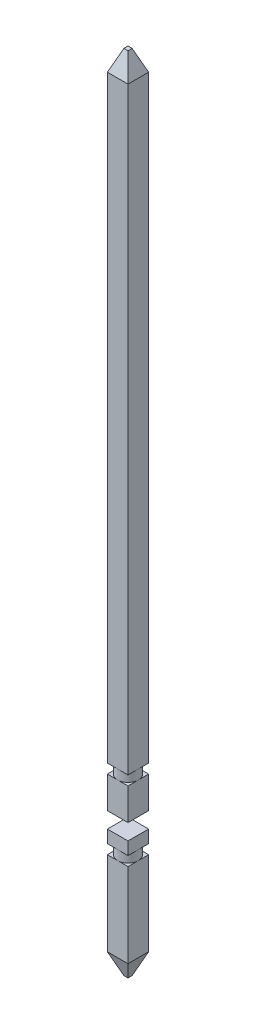
SolidWorks part; units mm, degrees
ref_plane "Front Plane" through (0, 0, 0) normal (0, 0, 1) x (1, 0, 0)
ref_plane "Top Plane" through (0, 0, 0) normal (0, 1, 0) x (1, 0, 0)
ref_plane "Right Plane" through (0, 0, 0) normal (1, 0, 0) x (0, 0, -1)
sketch "Sketch2" plane through (0, 0, 0) normal (0, 1, 0) x (1, 0, 0)
  line L1 (-0.325, -0.325) -> (0.325, -0.325)
  line L2 (-0.325, -0.325) -> (-0.325, 0.325)
  line L3 (-0.325, 0.325) -> (0.325, 0.325)
  line L4 (0.325, -0.325) -> (0.325, 0.325)
  line L5 (-0.325, -0.325) -> (0.325, 0.325) construction
  line L6 (-0.325, 0.325) -> (0.325, -0.325) construction
  point P0 (0, 0)
  dimension "D1" = 0.65
  dimension "D2" = 0.65
extrude "Boss-Extrude1" add sketch "Sketch2" along normal blind 25.3
sketch "Sketch6" plane through (0, 0, 0.325) normal (0, 0, 1) x (1, 0, 0)
  line L0 (-0.325, 25.3) -> (-0.325, 0) construction
  line L1 (-0.325, 4.5) -> (0.325, 4.5)
  line L2 (-0.325, 4.5) -> (-0.325, 4)
  line L3 (-0.325, 4) -> (0.325, 4)
  line L4 (0.325, 4.5) -> (0.325, 4)
  line L5 (0.325, 25.3) -> (0.325, 0) construction
  line L6 (-0.325, 0) -> (0.325, 0) construction
  dimension "D1" = 4
  dimension "D2" = 0.5
extrude "Cut-Extrude1" cut sketch "Sketch6" against normal through all
sketch "Sketch7" plane through (0, 0, 0.325) normal (0, 0, 1) x (1, 0, 0)
  line L0 (-0.325, 4) -> (-0.325, 0) construction
  line L1 (-0.325, 3.3) -> (0.325, 3.3)
  line L2 (-0.325, 3.3) -> (-0.325, 3.6)
  line L3 (-0.325, 3.6) -> (0.325, 3.6)
  line L4 (0.325, 3.3) -> (0.325, 3.6)
  line L5 (0.325, 4) -> (0.325, 0) construction
  line L7 (-0.325, 4) -> (0.325, 4) construction
  dimension "D1" = 0.3
  dimension "D2" = 0.4
extrude "Cut-Extrude2" cut sketch "Sketch7" against normal through all
sketch "Sketch8" plane through (0, 3.3, 0) normal (0, 1, 0) x (1, 0, 0)
  circle A0 centre (0, 0) radius 0.325
extrude "Boss-Extrude2" add sketch "Sketch8" along normal up to surface (0.3 mm away) up to face at (0, 3.6, 0)
sketch "Sketch9" plane through (0, 0, 0.325) normal (0, 0, 1) x (1, 0, 0)
  line L0 (-0.325, 25.3) -> (-0.325, 4.5) construction
  line L1 (-0.325, 5.5) -> (0.325, 5.5)
  line L2 (-0.325, 5.5) -> (-0.325, 5.8)
  line L3 (-0.325, 5.8) -> (0.325, 5.8)
  line L4 (0.325, 5.5) -> (0.325, 5.8)
  line L5 (0.325, 25.3) -> (0.325, 4.5) construction
  line L6 (0.325, 4.5) -> (-0.325, 4.5) construction
  dimension "D1" = 1
  dimension "D2" = 0.3
extrude "Cut-Extrude3" cut sketch "Sketch9" against normal through all
sketch "Sketch10" plane through (0, 5.5, 0) normal (0, 1, 0) x (1, 0, 0)
  circle A0 centre (0, 0) radius 0.325
extrude "Boss-Extrude3" add sketch "Sketch10" along normal up to surface (0.3 mm away) up to face at (0, 5.8, 0)
chamfer "Chamfer1" distance 0.65 distance2 0.26 4 edges at (0, 25.3, -0.325) (-0.325, 25.3, 0) (0, 25.3, 0.325) (0.325, 25.3, 0)
chamfer "Chamfer2" distance 0.26 distance2 0.65 4 edges at (0, 0, -0.325) (-0.325, 0, 0) (0, 0, 0.325) (0.325, 0, 0)
fillet "Fillet1" [suppressed] radius 0.01
fillet "Fillet2" [suppressed] radius 0.01
